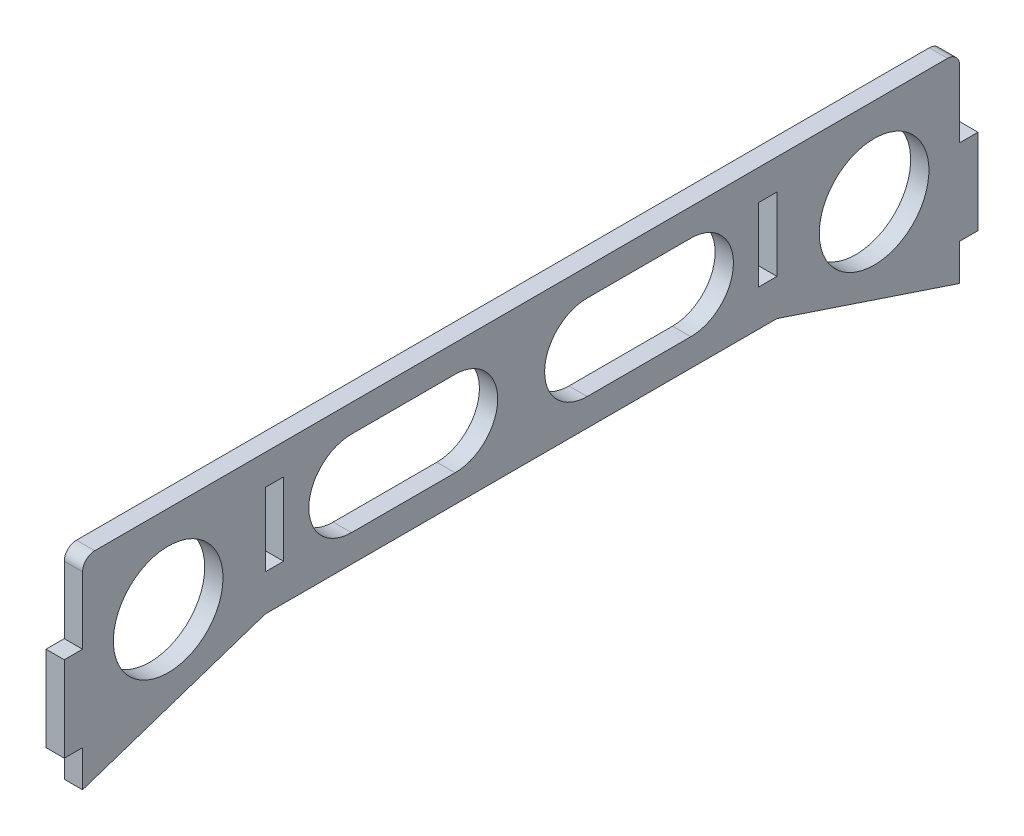
SolidWorks part; units mm, degrees
ref_plane "Front Plane" through (0, 0, 0) normal (0, 0, 1) x (1, 0, 0)
ref_plane "Top Plane" through (0, 0, 0) normal (0, 1, 0) x (1, 0, 0)
ref_plane "Right Plane" through (0, 0, 0) normal (1, 0, 0) x (0, 0, -1)
sketch "Sketch1" plane through (0, 0, 0) normal (1, 0, 0) x (0, 0, -1)
  line L1 (-72, -11.5) -> (72, -11.5)
  line L2 (-72, -11.5) -> (-72, 11.5)
  line L3 (-72, 11.5) -> (72, 11.5)
  line L4 (72, -11.5) -> (72, 11.5)
  line L5 (-72, -11.5) -> (72, 11.5) construction
  line L6 (-72, 11.5) -> (72, -11.5) construction
  point P0 (0, 0)
  dimension "D1" = 144
  dimension "D2" = 23
extrude "Boss-Extrude1" add sketch "Sketch1" along normal blind 3
fillet "Fillet1" radius 2 2 edges at (1.5, 11.5, -72) (1.5, 11.5, 72)
sketch "Sketch2" plane through (3, 0, 0) normal (1, 0, 0) x (0, 0, -1)
  line L0 (-72, -11.5) -> (-72, -21.5)
  line L1 (-72, -21.5) -> (-42, -11.5)
  line L2 (-72, -11.5) -> (72, -11.5) construction
  line L3 (72, -11.5) -> (72, -21.5)
  line L4 (72, -21.5) -> (42, -11.5)
  line L5 (-72, -11.5) -> (-42, -11.5)
  line L6 (42, -11.5) -> (72, -11.5)
  dimension "D1" = 10
  dimension "D2" = 30
  dimension "D3" = 30
  dimension "D4" = 10
extrude "Boss-Extrude2" add sketch "Sketch2" against normal blind 3
sketch "Sketch3" plane through (3, 0, 0) normal (1, 0, 0) x (0, 0, -1)
  line L0 (-72, 9.5) -> (-72, -21.5) construction
  line L1 (-72, -1.5) -> (-75, -1.5)
  line L2 (-72, -1.5) -> (-72, -15.5)
  line L3 (-72, -15.5) -> (-75, -15.5)
  line L4 (-75, -1.5) -> (-75, -15.5)
  line L5 (0, 1.65) -> (0, -1.65) construction
  line L6 (72, -15.5) -> (75, -15.5)
  line L7 (75, -1.5) -> (75, -15.5)
  line L8 (72, -1.5) -> (75, -1.5)
  line L9 (72, -1.5) -> (72, -15.5)
  dimension "D1" = 3
  dimension "D2" = 6
  dimension "D3" = 14
extrude "Boss-Extrude3" add sketch "Sketch3" against normal up to surface (3 mm away) up to face at (0, -2.8964, 0)
sketch "Sketch4" plane through (3, 0, 0) normal (1, 0, 0) x (0, 0, -1)
  line L0 (70, 11.5) -> (-70, 11.5) construction
  line L1 (-42, 6.5) -> (-39, 6.5)
  line L2 (-42, 6.5) -> (-42, -5.5)
  line L3 (-42, -5.5) -> (-39, -5.5)
  line L4 (-39, 6.5) -> (-39, -5.5)
  line L5 (0, 1.65) -> (0, -1.65) construction
  line L6 (42, -5.5) -> (39, -5.5)
  line L7 (39, 6.5) -> (39, -5.5)
  line L8 (42, 6.5) -> (39, 6.5)
  line L9 (42, 6.5) -> (42, -5.5)
  line L10 (-27.8515, 0) -> (-10.8515, 0) construction
  line L11 (1.65, 0) -> (-1.65, 0) construction
  line L12 (-27.8515, 7) -> (-10.8515, 7)
  line L13 (-27.8515, -7) -> (-10.8515, -7)
  line L14 (27.8515, 0) -> (10.8515, 0) construction
  line L15 (27.8515, 7) -> (10.8515, 7)
  line L16 (27.8515, -7) -> (10.8515, -7)
  circle A0 centre (-57.9425, -2.8753) radius 9
  arc A1 (-27.8515, 7) -> (-27.8515, -7) centre (-27.8515, 0) ccw
  arc A2 (-10.8515, -7) -> (-10.8515, 7) centre (-10.8515, 0) ccw
  arc A3 (27.8515, 7) -> (27.8515, -7) centre (27.8515, 0) cw
  arc A4 (10.8515, -7) -> (10.8515, 7) centre (10.8515, 0) cw
  circle A5 centre (57.9425, -2.8753) radius 9
  point P19 (-19.3515, 0)
  point P24 (-9.8198, 0)
  point P27 (19.3515, 0)
  dimension "D5" = 18
  dimension "D6" = 7
  dimension "D1" = 12
  dimension "D2" = 5
  dimension "D3" = 3
  dimension "D4" = 39
  dimension "D7" = 17
extrude "Cut-Extrude1" cut sketch "Sketch4" against normal blind 10
